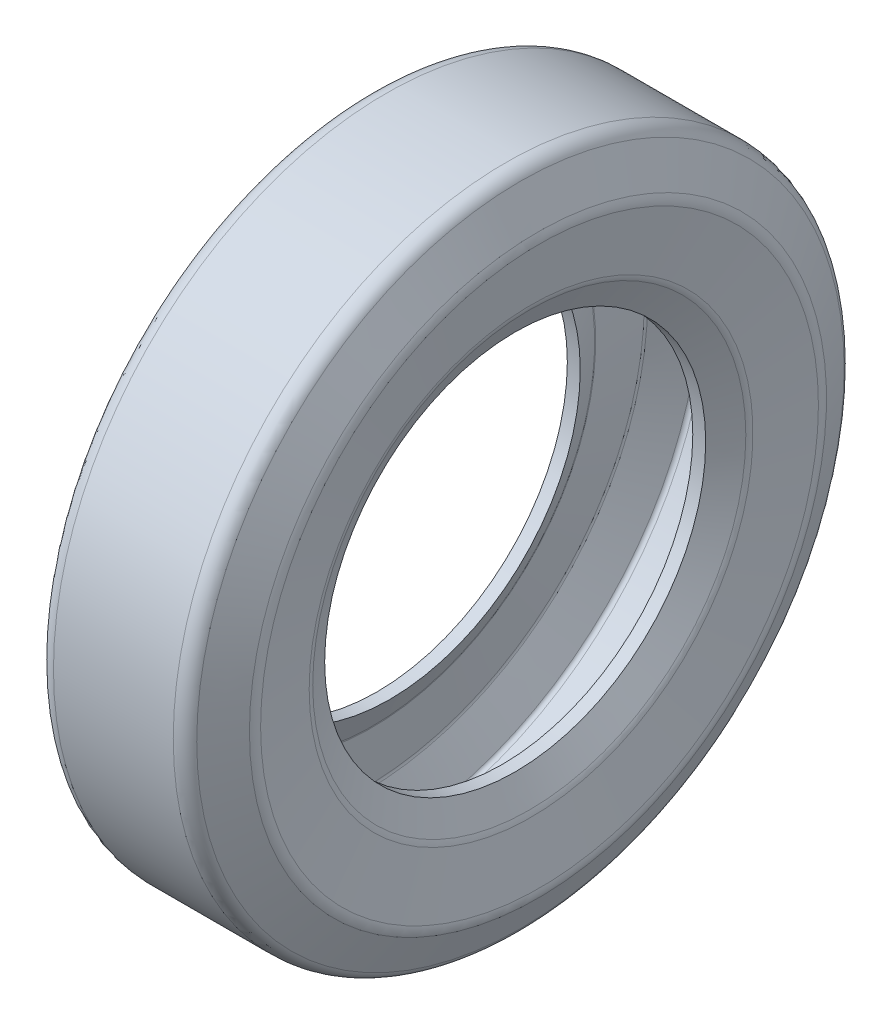
SolidWorks part; units mm, degrees
material "SANTOPRENE"
ref_plane "Front Plane" through (0, 0, 0) normal (0, 0, 1) x (1, 0, 0)
ref_plane "Top Plane" through (0, 0, 0) normal (0, 1, 0) x (1, 0, 0)
ref_plane "Right Plane" through (0, 0, 0) normal (1, 0, 0) x (0, 0, -1)
sketch "Sketch1" plane through (0, 0, 0) normal (0, 1, 0) x (1, 0, 0)
  line L0 (-234.4961, 0) -> (234.4961, 0) construction
  line L1 (-36.9098, 205) -> (36.9098, 205)
  line L2 (45.8541, 199.4721) -> (56.6801, 177.8201)
  line L3 (57.6277, 171.8811) -> (52.4172, 136.7442)
  line L4 (0, 0) -> (0, 205) construction
  line L5 (51.319, 133.4495) -> (42.6353, 117.4128)
  line L6 (-51.319, 133.4495) -> (-42.6353, 117.4128)
  line L7 (-57.6277, 171.8811) -> (-52.4172, 136.7442)
  line L8 (-45.8541, 199.4721) -> (-56.6801, 177.8201)
  line L9 (-42.6353, 117.4128) -> (42.6353, 117.4128)
  arc A0 (52.4172, 136.7442) -> (51.319, 133.4495) centre (42.5254, 138.2111) cw
  arc A1 (36.9098, 205) -> (45.8541, 199.4721) centre (36.9098, 195) cw
  arc A2 (56.6801, 177.8201) -> (57.6277, 171.8811) centre (47.7358, 173.348) cw
  arc A3 (-56.6801, 177.8201) -> (-57.6277, 171.8811) centre (-47.7358, 173.348) ccw
  arc A4 (-36.9098, 205) -> (-45.8541, 199.4721) centre (-36.9098, 195) ccw
  arc A5 (-52.4172, 136.7442) -> (-51.319, 133.4495) centre (-42.5254, 138.2111) ccw
  point P4 (0, 0)
  point P8 (0, 205)
  point P15 (52.1586, 135)
  point P18 (43.0902, 205)
  point P21 (58.0902, 175)
  point P31 (-58.0902, 175)
  point P32 (-43.0902, 205)
  point P33 (-52.1586, 135)
  dimension "D8" = 10
  dimension "D1" = 30
  dimension "D2" = 15
  dimension "D3" = 145
  dimension "D4" = 20
  dimension "D5" = 160
  dimension "D6" = 70
  dimension "D7" = 80
  dimension "D9" = 205
revolve "Revolve1" add sketch "Sketch1" angle 360 about L0
shell "Shell1" thickness 7
